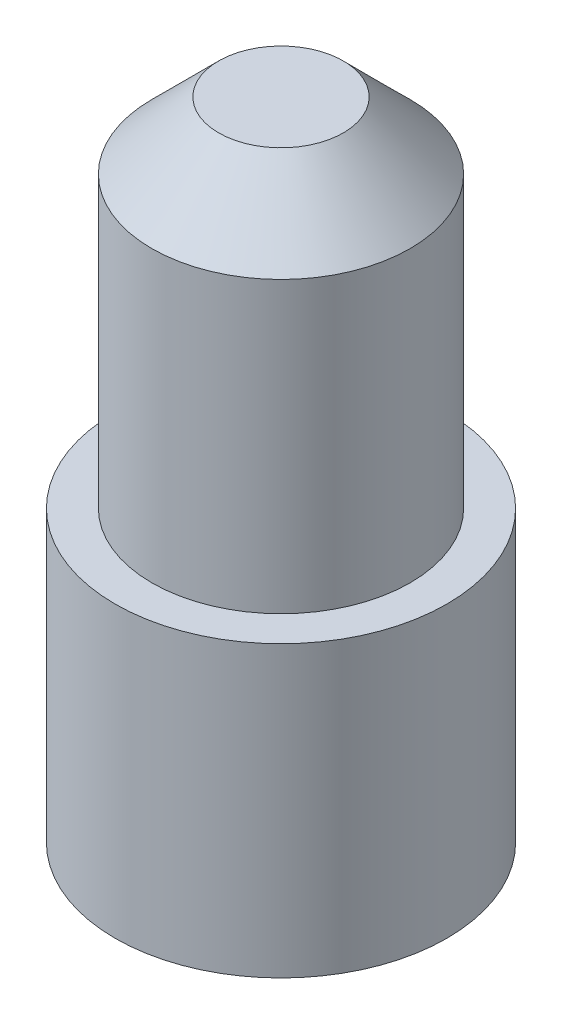
SolidWorks part; units mm, degrees
material "Maple"
ref_plane "Wasteboard" through (0, 0, 0) normal (0, 0, 1) x (1, 0, 0)
ref_plane "Left-Right" through (0, 0, 0) normal (0, 1, 0) x (1, 0, 0)
ref_plane "Front-Back" through (0, 0, 0) normal (1, 0, 0) x (0, 0, -1)
sketch "Sketch1" plane through (0, 0, 0) normal (0, 0, 1) x (1, 0, 0)
  line L0 (0, 19.9583) -> (0, -25.5417) construction
  line L1 (-3.725, -15.625) -> (3.725, -15.625)
  line L2 (3.725, -15.625) -> (3.725, -9.125)
  line L3 (3.725, -9.125) -> (2.9, -9.125)
  line L4 (2.9, -9.125) -> (2.9, -2.625)
  line L5 (1.4, -1.125) -> (-1.4, -1.125)
  line L6 (-2.9, -9.125) -> (-2.9, -2.625)
  line L7 (-3.725, -9.125) -> (-2.9, -9.125)
  line L8 (-3.725, -15.625) -> (-3.725, -9.125)
  line L9 (2.9, -2.625) -> (1.4, -1.125)
  line L10 (-2.9, -2.625) -> (-1.4, -1.125)
  point P5 (-2.9, -1.125)
  point P8 (2.9, -1.125)
  point P10 (0, -1.125)
  point P13 (0, -15.625)
  dimension "D1" = 7.45
  dimension "D2" = 5.8
  dimension "D4" = 6.5
  dimension "D5" = 8
revolve "Revolve2" add sketch "Sketch1" angle 360 about L0
